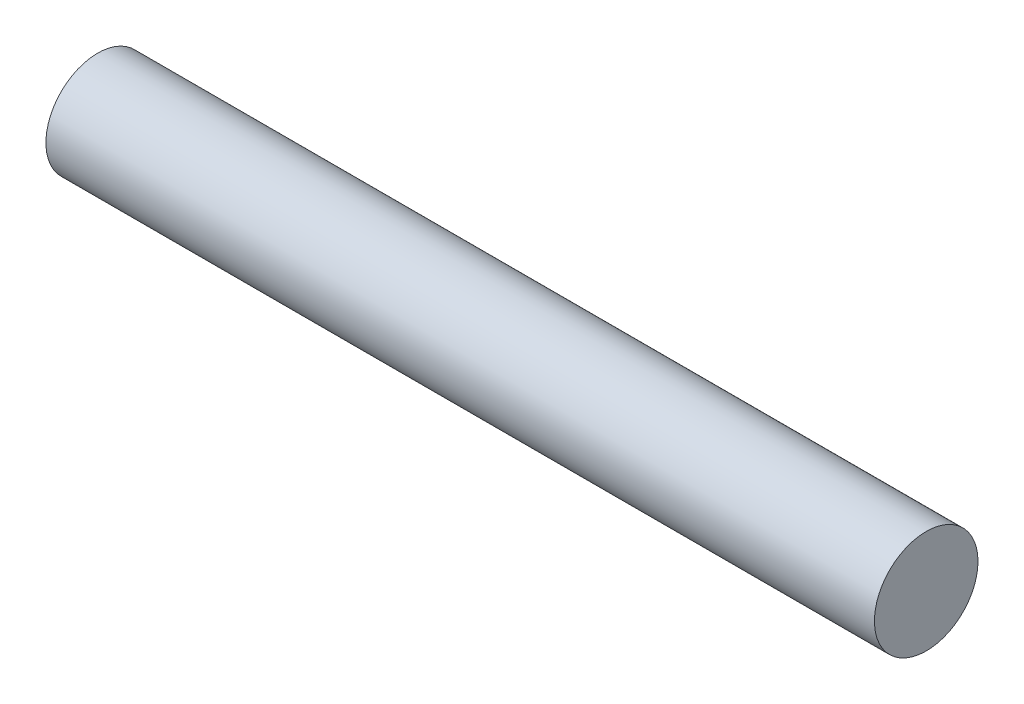
SolidWorks part; units mm, degrees
ref_plane "Front Plane" through (0, 0, 0) normal (0, 0, 1) x (1, 0, 0)
ref_plane "Top Plane" through (0, 0, 0) normal (0, 1, 0) x (1, 0, 0)
ref_plane "Right Plane" through (0, 0, 0) normal (1, 0, 0) x (0, 0, -1)
sketch "Sketch1" plane through (0, 0, 0) normal (1, 0, 0) x (0, 0, -1)
  circle A0 centre (0, 0) radius 5
  dimension "D1" = 10
extrude "Boss-Extrude1" add sketch "Sketch1" along normal blind 80
